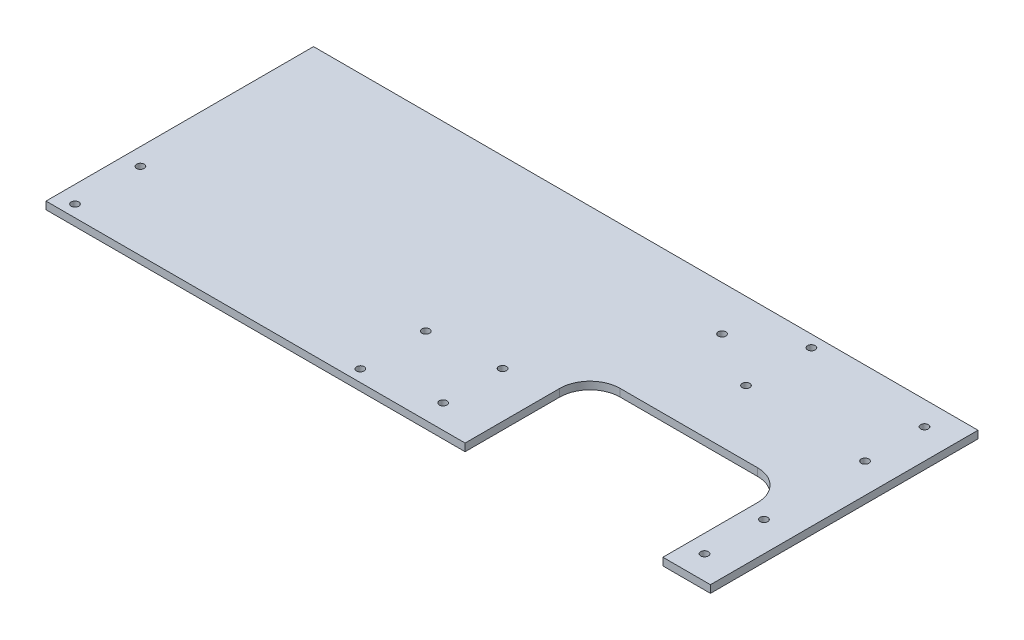
SolidWorks part; units mm, degrees
ref_plane "Front" through (0, 0, 0) normal (0, 0, 1) x (1, 0, 0)
ref_plane "Top" through (0, 0, 0) normal (0, 1, 0) x (1, 0, 0)
ref_plane "Right" through (0, 0, 0) normal (1, 0, 0) x (0, 0, -1)
sketch "Sketch1" plane through (0, 0, 0) normal (0, 1, 0) x (1, 0, 0)
  line L1 (-279.4, -112.5) -> (279.4, -112.5)
  line L2 (-279.4, -112.5) -> (-279.4, 112.5)
  line L3 (-279.4, 112.5) -> (279.4, 112.5)
  line L4 (279.4, -112.5) -> (279.4, 112.5)
  line L5 (-279.4, -112.5) -> (279.4, 112.5) construction
  line L6 (-279.4, 112.5) -> (279.4, -112.5) construction
  point P0 (0, 0)
  dimension "D1" = 558.8
  dimension "D2" = 225
extrude "Boss-Extrude1" add sketch "Sketch1" along normal blind 6.35
sketch "Sketch2" plane through (0, 6.35, 0) normal (0, 1, 0) x (1, 0, 0)
  line L0 (78.05, 1.2) -> (78.05, -151.2) construction
  line L1 (234.4, -151.2) -> (234.4, 1.2) construction
  line L2 (78.05, 1.2) -> (78.05, -151.2) construction
  line L3 (234.4, -151.2) -> (234.4, 1.2) construction
  line L4 (239.4, -30) -> (239.4, -105) construction
  line L5 (239.4, -7.5) -> (239.4, -151.2)
  line L6 (142.8719, -7.5) -> (158.8719, -7.5) construction
  line L7 (73.05, -7.5) -> (239.4, -7.5)
  line L8 (73.05, -7.5) -> (73.05, -151.2)
  line L9 (73.05, 1.2) -> (73.05, -151.2) construction
  line L10 (73.05, -151.2) -> (239.4, -151.2)
  dimension "D1" = 5
extrude "Cut-Extrude1" cut sketch "Sketch2" against normal through all
fillet "Fillet1" radius 25.4 2 edges at (239.4, 3.175, 7.5) (73.05, 3.175, 7.5)
sketch "Sketch3" plane through (0, 6.35, 0) normal (0, 1, 0) x (1, 0, 0)
  circle A0 centre (-265.0172, -102.5) radius 3.2 construction
  circle A1 centre (-265.0172, -47.5) radius 3.2 construction
  circle A2 centre (-25.0172, -47.5) radius 3.2 construction
  circle A3 centre (-25.0172, -102.5) radius 3.2 construction
  circle A4 centre (101.6441, 75) radius 3.2 construction
  circle A5 centre (149.2755, 102.5) radius 3.2 construction
  circle A6 centre (149.2755, 47.5) radius 3.2 construction
  circle A7 centre (254.4, 92.5) radius 3.2 construction
  circle A8 centre (254.4, 42.5) radius 3.2 construction
  circle A9 centre (254.4, -42.5) radius 3.2 construction
  circle A10 centre (254.4, -92.5) radius 3.2 construction
  circle A11 centre (-265.0172, -102.5) radius 3.2
  circle A12 centre (-265.0172, -47.5) radius 3.2
  circle A13 centre (-25.0172, -47.5) radius 3.2
  circle A14 centre (-25.0172, -102.5) radius 3.2
  circle A15 centre (101.6441, 75) radius 3.2
  circle A16 centre (149.2755, 102.5) radius 3.2
  circle A17 centre (149.2755, 47.5) radius 3.2
  circle A18 centre (254.4, 92.5) radius 3.2
  circle A19 centre (254.4, 42.5) radius 3.2
  circle A20 centre (254.4, -42.5) radius 3.2
  circle A21 centre (254.4, -92.5) radius 3.2
  circle A22 centre (34.575, -42.5) radius 3.2 construction
  circle A23 centre (34.575, -92.5) radius 3.2 construction
  circle A24 centre (34.575, -42.5) radius 3.2
  circle A25 centre (34.575, -92.5) radius 3.2
extrude "Cut-Extrude2" cut sketch "Sketch3" against normal through all
equation "\"in\"=10"
